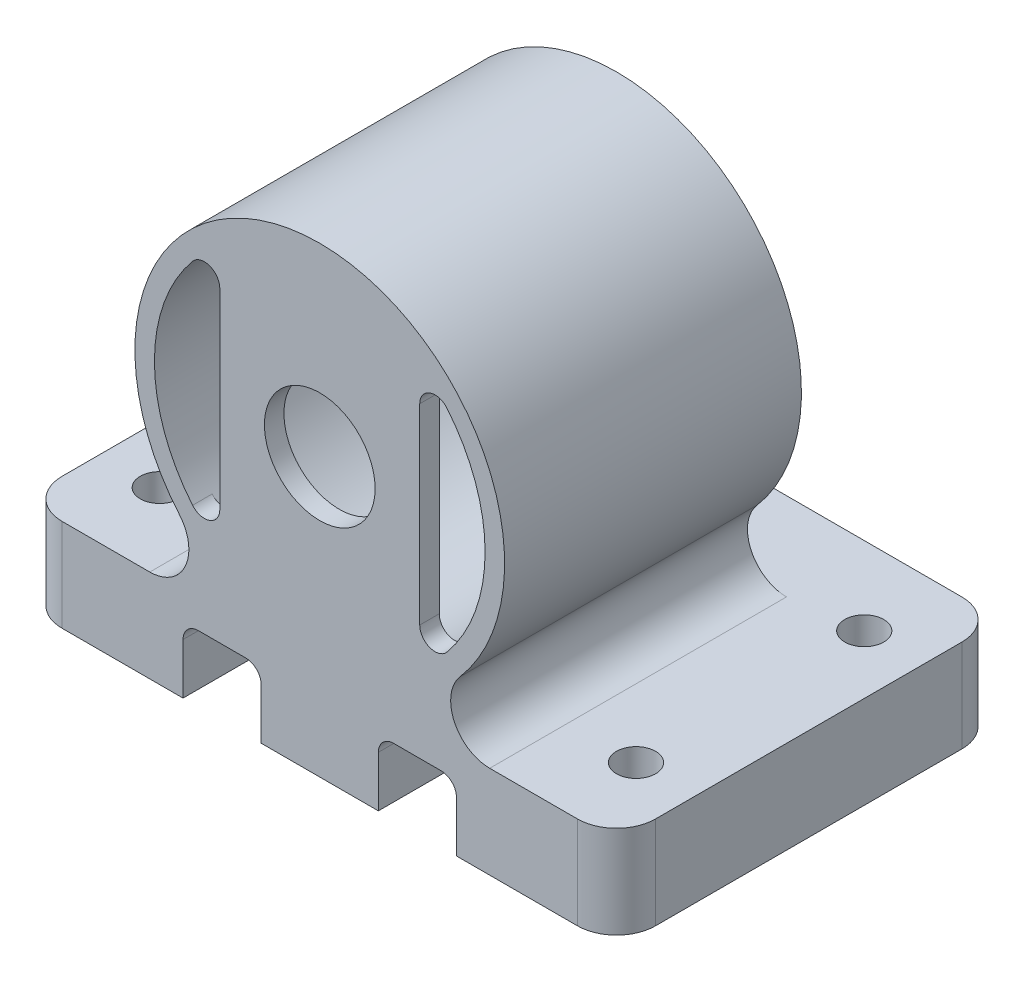
SolidWorks part; units mm, degrees
ref_plane "Front Plane" through (0, 0, 0) normal (0, 0, 1) x (1, 0, 0)
ref_plane "Top Plane" through (0, 0, 0) normal (0, 1, 0) x (1, 0, 0)
ref_plane "Right Plane" through (0, 0, 0) normal (1, 0, 0) x (0, 0, -1)
sketch "Sketch2" plane through (0, 0, 0) normal (0, 0, 1) x (1, 0, 0)
  circle A0 centre (0, 0) radius 10.75
  circle A1 centre (0, 0) radius 12.02
  dimension "D1" = 21.5
  dimension "D2" = 1.27
extrude "Boss-Extrude1" add sketch "Sketch2" along normal blind 19.3
sketch "Sketch3" plane through (0, 0, 19.3) normal (0, 0, 1) x (1, 0, 0)
  line L0 (-6.5, 0) -> (6.5, 0) construction
  line L2 (-6.5, -6.23) -> (-6.5, 6.23)
  line L4 (6.5, -6.23) -> (6.5, 6.23)
  arc A6 (8.2692, 6.8689) -> (6.5, 6.23) centre (7.5, 6.23) ccw
  arc A7 (8.2692, -6.8689) -> (6.5, -6.23) centre (7.5, -6.23) cw
  arc A8 (-6.5, -6.23) -> (-8.2692, -6.8689) centre (-7.5, -6.23) cw
  arc A9 (-6.5, 6.23) -> (-8.2692, 6.8689) centre (-7.5, 6.23) ccw
  circle A12 centre (0, 0) radius 3.6
  arc A16 (-8.2692, 6.8689) -> (8.2692, 6.8689) centre (0, 0) cw
  arc A17 (8.2692, -6.8689) -> (-8.2692, -6.8689) centre (0, 0) cw
  dimension "D1" = 10.75
  dimension "D3" = 1
  dimension "D4" = 7.2
  dimension "D2" = 10.75
  dimension "D6" = 13
extrude "Boss-Extrude4" add sketch "Sketch3" against normal blind 1.27
ref_plane "Plane1" through (0, -12.02, 0) normal (0, 1, 0) x (1, 0, 0)
sketch "Sketch4" plane through (0, -12.02, 0) normal (0, 1, 0) x (1, 0, 0)
  line L0 (-12.02, -19.3) -> (12.02, -19.3) construction
  line L1 (-12.02, -19.3) -> (12.02, -19.3)
  line L2 (-12.02, -19.3) -> (-16.755, -19.3)
  line L3 (-19.295, -16.76) -> (-19.295, 3.16)
  line L4 (-16.755, 5.7) -> (16.755, 5.7)
  line L5 (19.295, 3.16) -> (19.295, -16.76)
  line L6 (16.755, -19.3) -> (12.02, -19.3)
  arc A0 (-16.755, -19.3) -> (-19.295, -16.76) centre (-16.755, -16.76) cw
  arc A1 (19.295, -16.76) -> (16.755, -19.3) centre (16.755, -16.76) cw
  arc A2 (16.755, 5.7) -> (19.295, 3.16) centre (16.755, 3.16) cw
  arc A3 (-19.295, 3.16) -> (-16.755, 5.7) centre (-16.755, 3.16) cw
  point P6 (0, 5.7)
  point P12 (19.295, -19.3)
  point P15 (19.295, 5.7)
  point P18 (-19.295, 5.7)
  dimension "D3" = 2.54
  dimension "D1" = 38.59
  dimension "D2" = 25
extrude "Boss-Extrude5" add sketch "Sketch4" against normal blind 6.02 separate body
ref_point "Point2" [suppressed]
sketch "Sketch5" plane through (0, 0, 19.3) normal (0, 0, 1) x (1, 0, 0)
  line L1 (-10, -12.02) -> (-11.0509, -12.02)
  line L2 (-10, -18.04) -> (10, -18.04)
  line L3 (11.0509, -12.02) -> (10, -12.02)
  line L4 (10.615, -12.02) -> (-10.615, -12.02) construction
  line L6 (-10, -12.02) -> (-10, -18.04)
  line L7 (10, -12.02) -> (10, -18.04)
  arc A0 (-9.1231, -7.8262) -> (9.1231, -7.8262) centre (0, 0) ccw
  arc A3 (11.0509, -12.02) -> (9.1231, -7.8262) centre (11.0509, -9.48) cw
  arc A4 (-11.0509, -12.02) -> (-9.1231, -7.8262) centre (-11.0509, -9.48) ccw
  point P0 (0, -12.02)
  point P4 (0, -18.04)
  dimension "D1" = 2.54
  dimension "D2" = 12.02
  dimension "D3" = 20
  dimension "D4" = 6.02
extrude "Boss-Extrude6" add sketch "Sketch5" against normal up to surface (19.3 mm away) up to face at (12.02, 0, 0)
sketch "Sketch6" plane through (0, 0, 19.3) normal (0, 0, 1) x (1, 0, 0)
  line L0 (-8.89, -18.04) -> (-8.89, -14.74)
  line L1 (-16.755, -18.04) -> (16.755, -18.04) construction
  line L2 (-7.89, -13.74) -> (-4.81, -13.74)
  line L3 (-3.81, -14.74) -> (-3.81, -18.04)
  line L4 (-3.81, -18.04) -> (-8.89, -18.04)
  line L5 (0, 0) -> (0, -18.04) construction
  line L6 (3.81, -14.74) -> (3.81, -18.04)
  line L7 (7.89, -13.74) -> (4.81, -13.74)
  line L8 (8.89, -18.04) -> (8.89, -14.74)
  line L9 (3.81, -18.04) -> (8.89, -18.04)
  arc A0 (-4.81, -13.74) -> (-3.81, -14.74) centre (-4.81, -14.74) cw
  arc A1 (-8.89, -14.74) -> (-7.89, -13.74) centre (-7.89, -14.74) cw
  arc A2 (4.81, -13.74) -> (3.81, -14.74) centre (4.81, -14.74) ccw
  arc A3 (8.89, -14.74) -> (7.89, -13.74) centre (7.89, -14.74) ccw
  dimension "D4" = 1
  dimension "D1" = 5.08
  dimension "D2" = 8.89
  dimension "D3" = 4.3
extrude "Cut-Extrude1" cut sketch "Sketch6" against normal through all
sketch "Sketch7" plane through (0, -18.04, 0) normal (0, -1, 0) x (1, 0, 0)
  line L0 (0, 19.3) -> (0, -5.7) construction
  line L1 (-3.81, 19.3) -> (3.81, 19.3) construction
  line L2 (3.81, -5.7) -> (-3.81, -5.7) construction
  line L3 (-19.295, 6.8) -> (19.295, 6.8) construction
  line L4 (-19.295, -3.16) -> (-19.295, 16.76) construction
  line L5 (19.295, 16.76) -> (19.295, -3.16) construction
  line L6 (-16.755, 19.3) -> (-8.89, 19.3) construction
  circle A0 centre (-15.485, 14.22) radius 1.27
  circle A1 centre (15.485, 14.22) radius 1.27
  circle A2 centre (-15.485, -0.62) radius 1.27
  circle A3 centre (15.485, -0.62) radius 1.27
  point P16 (-15.7537, 16.6031)
  dimension "D1" = 2.54
  dimension "D2" = 3.81
  dimension "D3" = 5.08
extrude "Cut-Extrude2" cut sketch "Sketch7" against normal through all
